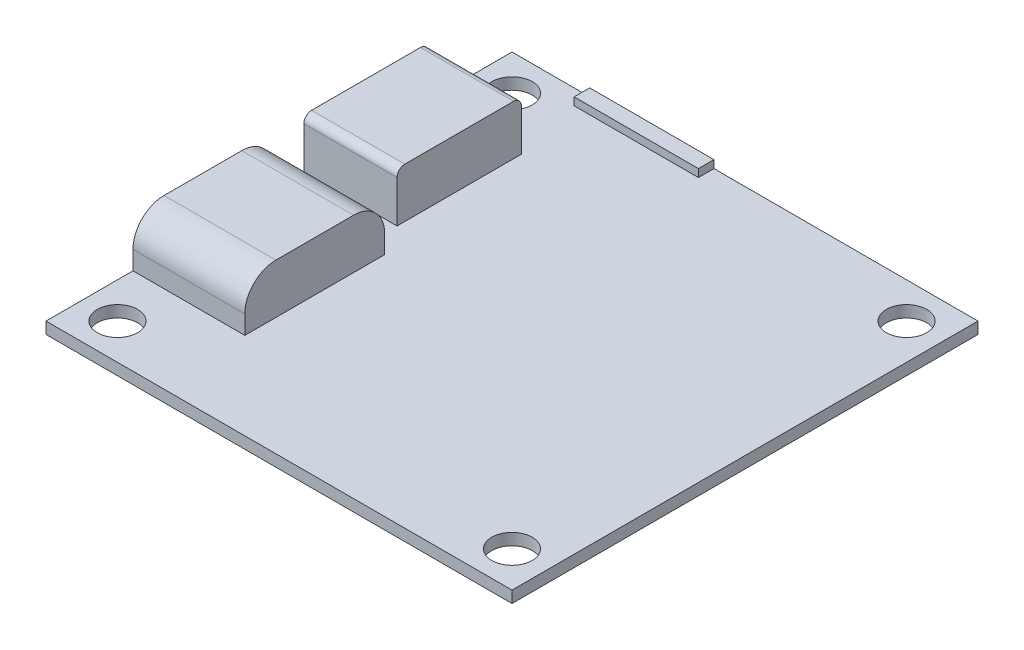
SolidWorks part; units mm, degrees
ref_plane "Front Plane" through (0, 0, 0) normal (0, 0, 1) x (1, 0, 0)
ref_plane "Top Plane" through (0, 0, 0) normal (0, 1, 0) x (1, 0, 0)
ref_plane "Right Plane" through (0, 0, 0) normal (1, 0, 0) x (0, 0, -1)
sketch "Sketch1" plane through (0, 0, 0) normal (0, 1, 0) x (1, 0, 0)
  line L1 (-15, 15) -> (15, 15)
  line L2 (-15, 15) -> (-15, -15)
  line L3 (-15, -15) -> (15, -15)
  line L4 (15, 15) -> (15, -15)
  line L5 (-15, 15) -> (15, -15) construction
  line L6 (-15, -15) -> (15, 15) construction
  point P0 (0, 0)
  dimension "D1" = 30
extrude "Boss-Extrude1" add sketch "Sketch1" along normal mid plane 0.75
sketch "Sketch2" plane through (0, 0.375, 0) normal (0, 1, 0) x (1, 0, 0)
  line L0 (-15, 15) -> (15, -15) construction
  line L2 (-15, 15) -> (-15, -15) construction
  line L4 (15, 15) -> (-15, 15) construction
  line L5 (-12.7, 14) -> (-10.9053, 14) construction
  circle A0 centre (-12.7, 12.7) radius 1.3
  dimension "D1" = 2.6
  dimension "D2" = 1
extrude "Cut-Extrude1" cut sketch "Sketch2" against normal through all
mirror "Mirror1" about plane through (0, 0, 0) normal (1, 0, 0) of "Cut-Extrude1"
mirror "Mirror2" about plane through (0, 0, 0) normal (0, 0, 1) of "Mirror1", "Cut-Extrude1"
sketch "Sketch3" plane through (0, 0.375, 0) normal (0, 1, 0) x (1, 0, 0)
  line L0 (-15, 15) -> (-15, -15) construction
  line L1 (-15, -9.4) -> (-7.8, -9.4)
  line L2 (-15, -9.4) -> (-15, -0.4)
  line L3 (-15, -0.4) -> (-7.8, -0.4)
  line L4 (-7.8, -9.4) -> (-7.8, -0.4)
  line L5 (-15, -15) -> (15, -15) construction
  line L6 (-15, 1.6) -> (-9, 1.6)
  line L7 (-15, 1.6) -> (-15, 9.6)
  line L8 (-15, 9.6) -> (-9, 9.6)
  line L9 (-9, 1.6) -> (-9, 9.6)
  dimension "D1" = 9
  dimension "D2" = 5.6
  dimension "D3" = 7.2
  dimension "D4" = 8
  dimension "D5" = 2
  dimension "D6" = 6
extrude "Boss-Extrude2" add sketch "Sketch3" along normal blind 3.2
fillet "Fillet1" radius 2 2 edges at (-11.4, 3.575, 0.4) (-11.4, 3.575, 9.4)
fillet "Fillet2" radius 0.5 2 edges at (-12, 3.575, -9.6) (-12, 3.575, -1.6)
sketch "Sketch4" plane through (0, 0.375, 0) normal (0, 1, 0) x (1, 0, 0)
  line L0 (15, 15) -> (-15, 15) construction
  line L1 (-10, 15) -> (-2, 15)
  line L2 (-10, 15) -> (-10, 14)
  line L3 (-10, 14) -> (-2, 14)
  line L4 (-2, 15) -> (-2, 14)
  line L5 (-15, 15) -> (-15, 9.6) construction
  dimension "D1" = 1
  dimension "D2" = 5
  dimension "D3" = 8
extrude "Boss-Extrude3" add sketch "Sketch4" along normal mid plane 1
